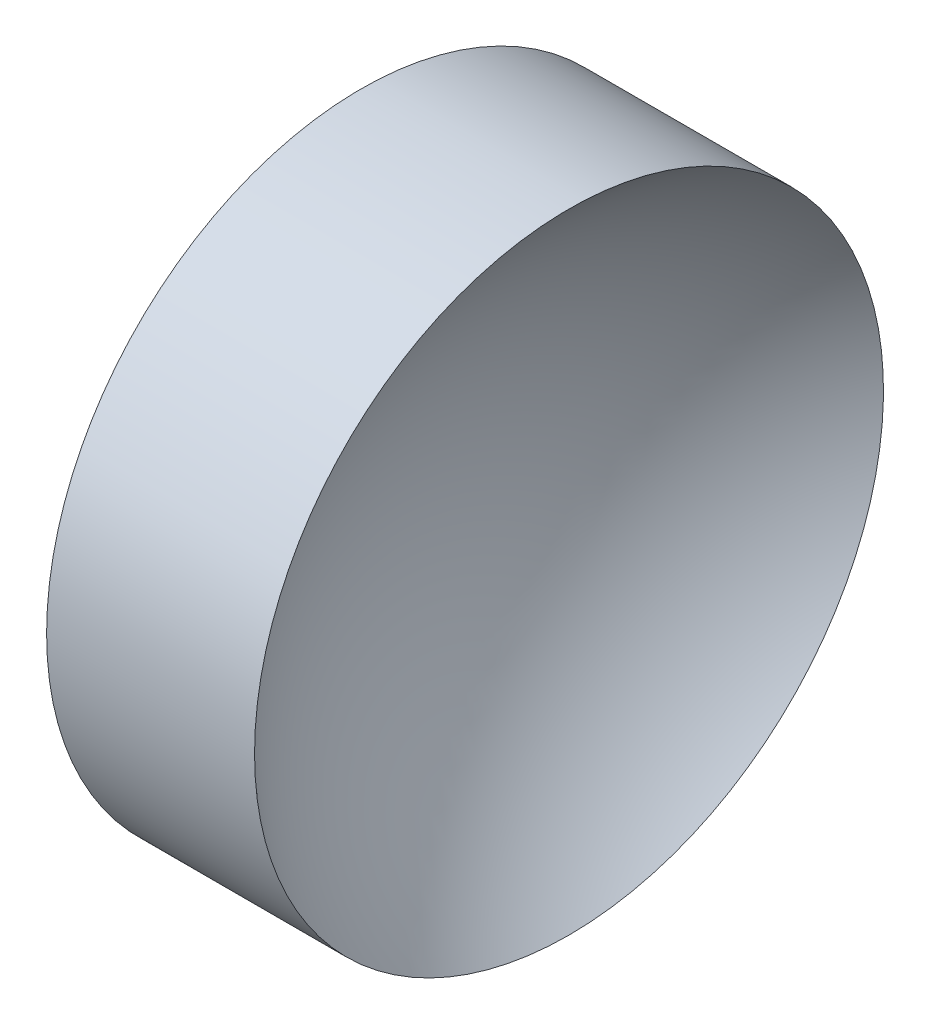
SolidWorks part; units mm, degrees
ref_plane "前视基准面" through (0, 0, 0) normal (0, 0, 1) x (1, 0, 0)
ref_plane "上视基准面" through (0, 0, 0) normal (0, 1, 0) x (1, 0, 0)
ref_plane "右视基准面" through (0, 0, 0) normal (1, 0, 0) x (0, 0, -1)
sketch "草图1" plane through (0, 0, 0) normal (0, 0, 1) x (1, 0, 0)
  line L0 (42.4499, 26.089) -> (50.324, 26.089) construction
  line L1 (44.3192, 26.089) -> (44.3192, 34.089)
  line L2 (45.8192, 26.089) -> (44.3192, 26.089)
  line L3 (44.3192, 34.089) -> (49.6092, 34.089)
  arc A0 (49.6092, 34.089) -> (45.8192, 26.089) centre (56.1574, 26.089) ccw
revolve "旋转1" add sketch "草图1" angle 360 about L0
